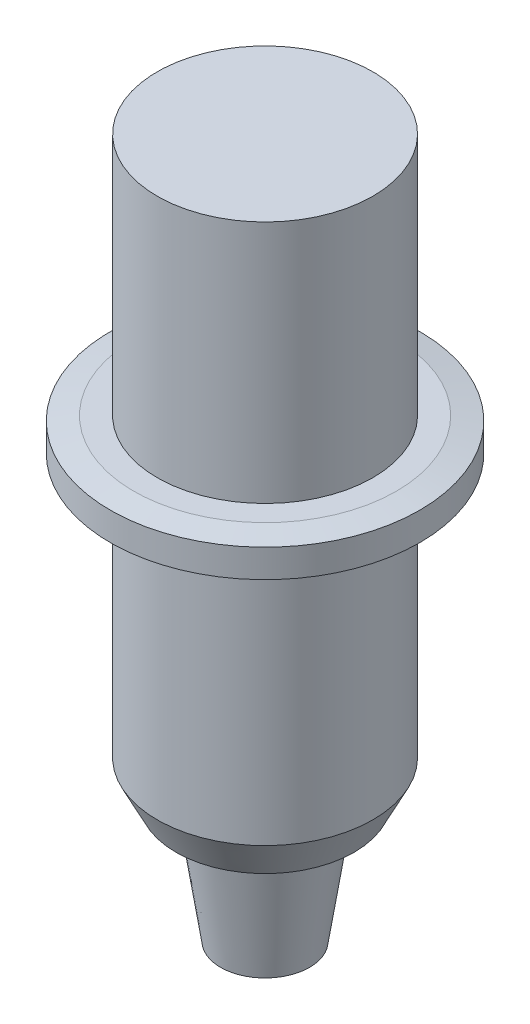
SolidWorks part; units mm, degrees
ref_plane "Front Plane" through (0, 0, 0) normal (0, 0, 1) x (1, 0, 0)
ref_plane "Top Plane" through (0, 0, 0) normal (0, 1, 0) x (1, 0, 0)
ref_plane "Right Plane" through (0, 0, 0) normal (1, 0, 0) x (0, 0, -1)
sketch "Sketch1" plane through (0, 0, 0) normal (0, 0, 1) x (1, 0, 0)
  line L0 (0, -143.9505) -> (0, 7053.5726) construction
  line L1 (0, 0) -> (2.375, 0)
  line L2 (2.375, 0) -> (3.2, 5.5)
  line L3 (3.2, 5.5) -> (3.2, 6.5)
  line L4 (3.2, 6.5) -> (4.75, 6.5)
  line L5 (4.75, 6.5) -> (5.75, 8.5)
  line L6 (5.75, 8.5) -> (5.75, 22.3)
  line L7 (5.75, 22.3) -> (7, 22.3)
  line L8 (7, 22.3) -> (8.25, 22.55)
  line L9 (8.25, 22.55) -> (8.25, 24.05)
  line L10 (8.25, 24.05) -> (7, 24.3)
  line L11 (7, 24.3) -> (5.75, 24.3)
  line L12 (5.75, 24.3) -> (5.75, 37.3)
  line L13 (5.75, 37.3) -> (0, 37.3)
  line L14 (0, 37.3) -> (0, 0)
  point P18 (0, 37.3)
  point P29 (0, 0)
  dimension "D2" = 15.8
  dimension "D3" = 11.5
  dimension "D4" = 2
  dimension "D5" = 1.5
  dimension "D6" = 16.5
  dimension "D7" = 6.5
  dimension "D8" = 1
  dimension "D9" = 6.4
  dimension "D10" = 4.75
  dimension "D11" = 2
  dimension "D12" = 1.25
  dimension "D13" = 13
  dimension "D14" = 9.5
revolve "5.63 mm bottom to pen tip" add sketch "Sketch1" angle 360 about L0
